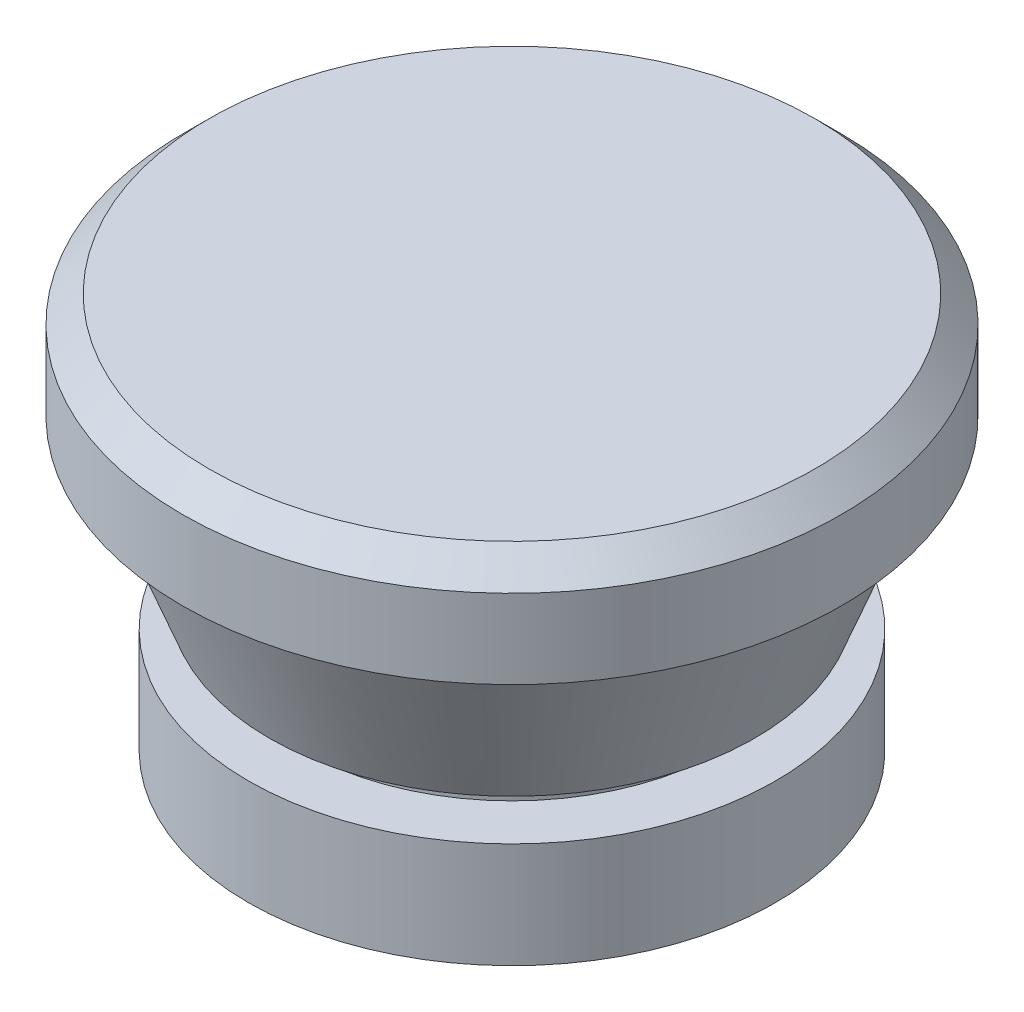
SolidWorks part; units mm, degrees
ref_plane "Front Plane" through (0, 0, 0) normal (0, 0, 1) x (1, 0, 0)
ref_plane "Top Plane" through (0, 0, 0) normal (0, 1, 0) x (1, 0, 0)
ref_plane "Right Plane" through (0, 0, 0) normal (1, 0, 0) x (0, 0, -1)
sketch "Sketch2" plane through (0, 0, 0) normal (0, 0, 1) x (1, 0, 0)
  line L0 (0, 0) -> (0, 15)
  line L1 (0, 15) -> (11.5, 15)
  line L2 (11.5, 15) -> (12.5, 14)
  line L3 (12.5, 14) -> (12.5, 11)
  line L4 (12.5, 11) -> (11.5, 11)
  line L5 (11.5, 11) -> (9.2027, 5)
  line L6 (9.2027, 5) -> (8, 5)
  line L7 (8, 5) -> (8, 4)
  line L8 (8, 4) -> (10, 4)
  line L9 (10, 4) -> (10, 0)
  line L10 (10, 0) -> (0, 0)
  line L11 (0, 15) -> (50000, 15) construction
  dimension "D1" = 15
  dimension "D2" = 11.5
  dimension "D3" = 12.5
  dimension "D4" = 45
  dimension "D5" = 3
  dimension "D6" = 1
  dimension "D7" = 1
  dimension "D8" = 4
  dimension "D9" = 10
  dimension "D10" = 8
ref_axis "Axis1" through (0, 15.75, 0) along (0, -1, 0)
revolve "Revolve1" add sketch "Sketch2" angle 360 about axis through (0, 15.75, 0) along (0, -1, 0)
sketch "Sketch3" plane through (0, 0, 0) normal (0, -1, 0) x (1, 0, 0)
  circle A0 centre (0, 0) radius 5.5
  dimension "D1" = 11
extrude "Cut-Extrude1" cut sketch "Sketch3" against normal blind 3
